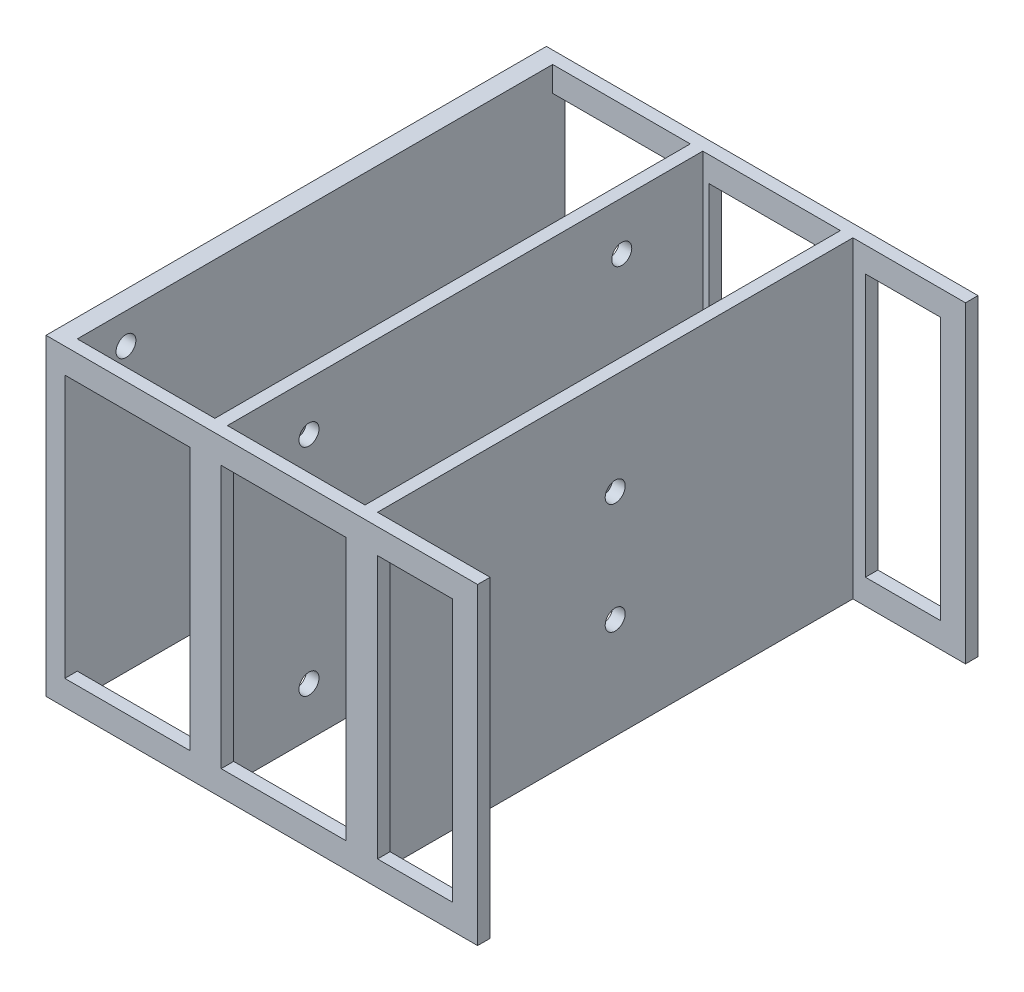
SolidWorks part; units mm, degrees
ref_plane "前视基准面" through (0, 0, 0) normal (0, 0, 1) x (1, 0, 0)
ref_plane "上视基准面" through (0, 0, 0) normal (0, 1, 0) x (1, 0, 0)
ref_plane "右视基准面" through (0, 0, 0) normal (1, 0, 0) x (0, 0, -1)
sketch "草图1" plane through (0, 0, 0) normal (0, 1, 0) x (1, 0, 0)
  line L0 (0, 0) -> (0, 80) construction
  line L1 (0, 0) -> (69, 0)
  line L3 (3, 2) -> (25, 2)
  line L4 (69, 0) -> (69, 2)
  line L5 (0, 80) -> (0, 0)
  line L6 (0, 80) -> (69, 80)
  line L8 (3, 78) -> (25, 78)
  line L9 (69, 80) -> (69, 78)
  line L13 (3, 78) -> (3, 2)
  line L14 (27, 78) -> (49, 78)
  line L16 (25, 78) -> (25, 2)
  line L18 (27, 78) -> (27, 2)
  line L20 (49, 78) -> (49, 2)
  line L22 (51, 78) -> (51, 2)
  line L23 (51, 78) -> (69, 78)
  line L24 (27, 2) -> (49, 2)
  line L25 (51, 2) -> (69, 2)
  dimension "D1" = 3
  dimension "D3" = 80
  dimension "D4" = 2
  dimension "D5" = 2
  dimension "D6" = 22
  dimension "D7" = 2
  dimension "D8" = 22
  dimension "D9" = 2
  dimension "D10" = 18
extrude "凸台-拉伸1" add sketch "草图1" along normal blind 50
sketch "草图2" plane through (51, 0, 0) normal (1, 0, 0) x (0, 0, -1)
  circle A0 centre (40, 33.85) radius 1.6
  circle A1 centre (40, 16.15) radius 1.6
sketch "草图3" plane through (27, 0, 0) normal (1, 0, 0) x (0, 0, -1)
  circle A0 centre (15.0463, 7.75) radius 1.6
  circle A1 centre (65.0463, 7.75) radius 1.6
  circle A2 centre (15.0463, 42.25) radius 1.6
  circle A3 centre (65.0463, 42.25) radius 1.6
sketch "草图4" plane through (3, 0, 0) normal (1, 0, 0) x (0, 0, -1)
  line L0 (40, 50) -> (40, 37.1382) construction
  line L1 (2, 50) -> (78, 50) construction
  line L2 (2, 25) -> (15.3072, 25) construction
  line L3 (2, 50) -> (2, 0) construction
  line L4 (78, 50) -> (78, 0) construction
  circle A0 centre (69.782, 5.121) radius 1.587
  circle A1 centre (9.782, 45.121) radius 1.587
  circle A2 centre (76, 48) radius 1.6 construction
  circle A3 centre (4, 48) radius 1.6 construction
  circle A4 centre (76, 2) radius 1.6 construction
  circle A5 centre (4, 2) radius 1.6 construction
  dimension "D1" = 3.2
  dimension "D2" = 2
  dimension "D3" = 2
sketch "草图5" plane through (0, 0, 0) normal (0, 0, 1) x (1, 0, 0)
  line L1 (3, 46) -> (23, 46)
  line L2 (3, 46) -> (3, 4)
  line L3 (3, 4) -> (23, 4)
  line L4 (23, 46) -> (23, 4)
  line L5 (28, 46) -> (48, 46)
  line L6 (28, 46) -> (28, 4)
  line L7 (28, 4) -> (48, 4)
  line L8 (48, 46) -> (48, 4)
  line L9 (53, 46) -> (65, 46)
  line L10 (53, 46) -> (53, 4)
  line L11 (53, 4) -> (65, 4)
  line L12 (65, 46) -> (65, 4)
  line L13 (0, 25) -> (74.6996, 25) construction
  line L14 (0, 50) -> (0, 0) construction
  line L15 (0, 50) -> (69, 50) construction
  dimension "D1" = 20
  dimension "D2" = 3
  dimension "D3" = 5
  dimension "D4" = 5
  dimension "D5" = 4
  dimension "D6" = 4
  dimension "D7" = 4
  dimension "D8" = 20
  dimension "D9" = 12
extrude "切除-拉伸1" cut sketch "草图5" against normal blind 10
ref_plane "基准面1" through (0, 0, -40) normal (0, 0, 1) x (1, 0, 0)
mirror "镜向1" about plane through (0, 0, -40) normal (0, 0, 1) of "切除-拉伸1"
extrude "切除-拉伸2" cut sketch "草图2" against normal blind 10
extrude "切除-拉伸3" cut sketch "草图3" against normal blind 10
extrude "切除-拉伸4" cut sketch "草图4" against normal blind 10
